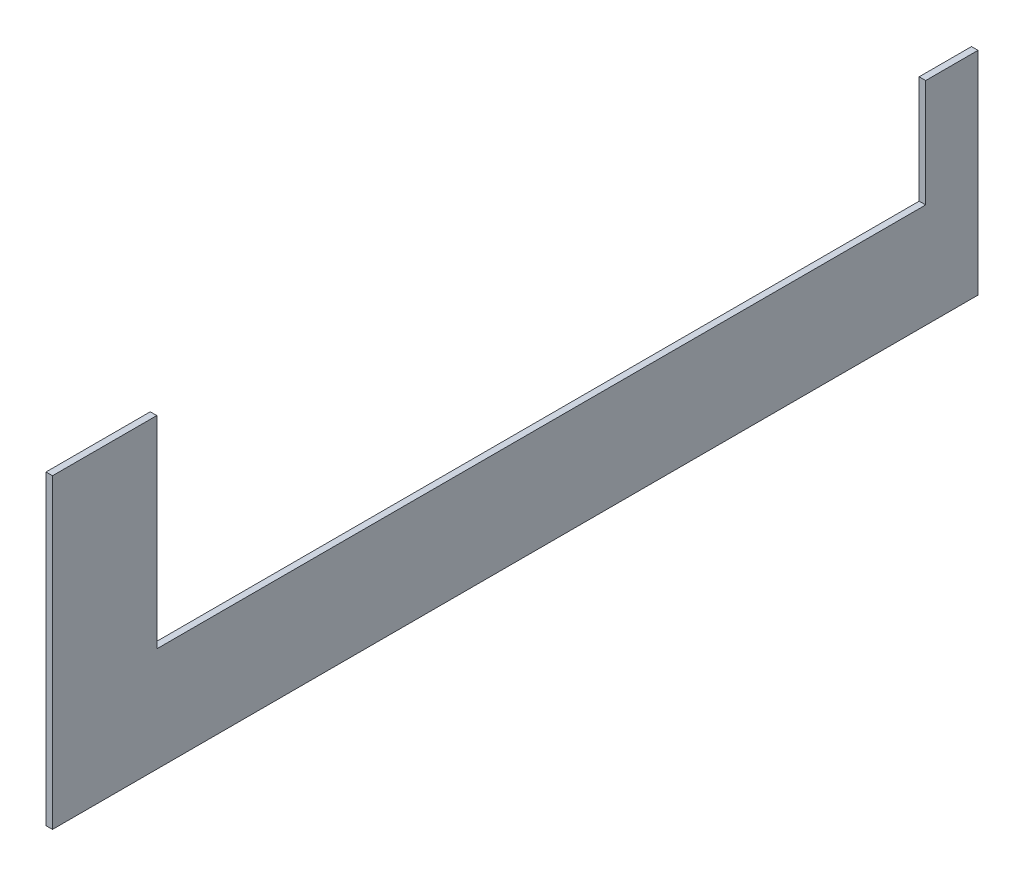
SolidWorks part; units mm, degrees
ref_plane "Front Plane" through (0, 0, 0) normal (0, 0, 1) x (1, 0, 0)
ref_plane "Top Plane" through (0, 0, 0) normal (0, 1, 0) x (1, 0, 0)
ref_plane "Right Plane" through (0, 0, 0) normal (1, 0, 0) x (0, 0, -1)
sketch "Sketch1" plane through (0, 0, 0) normal (1, 0, 0) x (0, 0, -1)
  line L0 (-225.425, 0) -> (225.425, 0)
  line L1 (-225.425, 0) -> (-225.425, 149.225)
  line L2 (-225.425, 149.225) -> (-174.625, 149.225)
  line L3 (-174.625, 149.225) -> (-174.625, 50.8)
  line L4 (-174.625, 50.8) -> (199.9261, 50.8)
  line L5 (199.9261, 50.8) -> (199.9261, 103.276)
  line L6 (199.9261, 103.276) -> (225.425, 103.276)
  line L7 (225.425, 103.276) -> (225.425, 0)
  point P3 (0, 0)
  dimension "D1" = 450.85
  dimension "D2" = 50.8
  dimension "D3" = 98.425
  dimension "D4" = 50.8
extrude "Boss-Extrude1" add sketch "Sketch1" along normal blind 3.175
